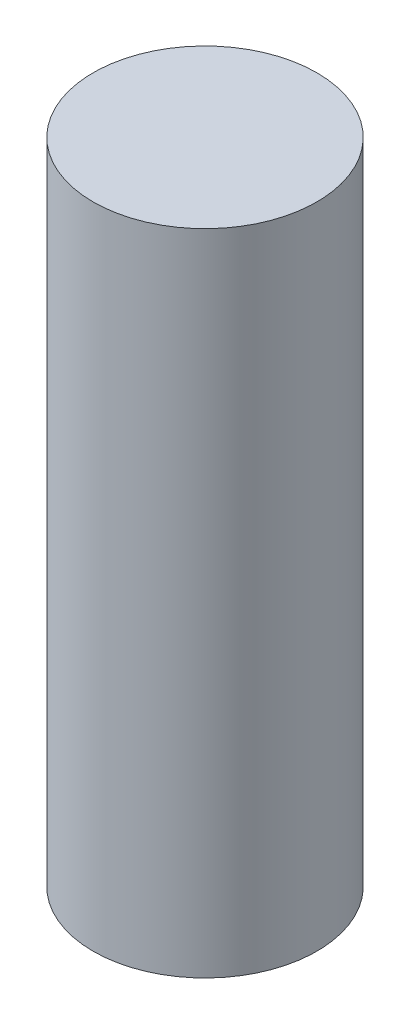
SolidWorks part; units mm, degrees
ref_plane "Alzado" through (0, 0, 0) normal (0, 0, 1) x (1, 0, 0)
ref_plane "Planta" through (0, 0, 0) normal (0, 1, 0) x (1, 0, 0)
ref_plane "Vista lateral" through (0, 0, 0) normal (1, 0, 0) x (0, 0, -1)
sketch "Croquis1" plane through (0, 0, 0) normal (0, 1, 0) x (1, 0, 0)
  circle A0 centre (0, 0) radius 2.5
  dimension "D1" = 5
extrude "Saliente-Extruir1" add sketch "Croquis1" along normal blind 14.5
